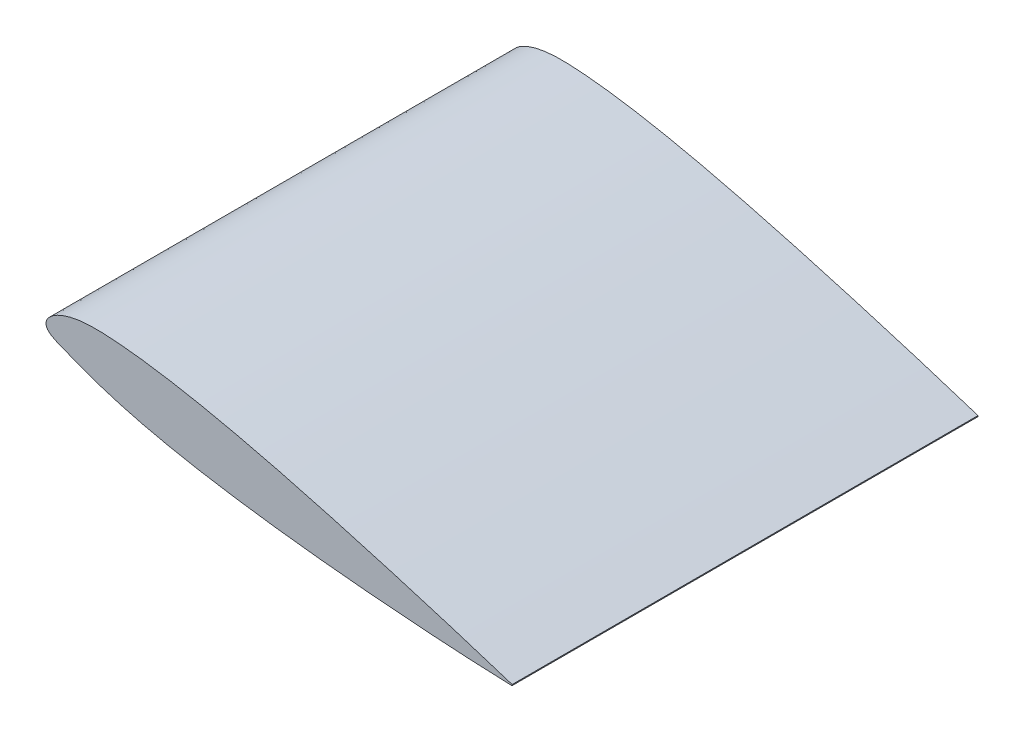
SolidWorks part; units mm, degrees
ref_plane "Płaszczyzna przednia"
ref_plane "Płaszczyzna górna" through (0, 0, 0) normal (0, 1, 0) x (1, 0, 0)
ref_plane "Płaszczyzna prawa" through (0, 0, 0) normal (1, 0, 0) x (0, 0, -1)
curve "Krzywa1"
  spline degree 3 poles (1, 0.0013, 0) (0.9998, 0.0013, 0) (0.9989, 0.0014, 0) (0.9968, 0.0017, 0) (0.9934, 0.0022, 0) (0.9886, 0.0029, 0) (0.9826, 0.0038, 0) (0.9751, 0.0049, 0) (0.9664, 0.0061, 0) (0.9564, 0.0076, 0) (0.9452, 0.0092, 0) (0.9327, 0.0109, 0) (0.9191, 0.0128, 0) (0.9043, 0.0148, 0) (0.8884, 0.017, 0) (0.8714, 0.0192, 0) (0.8535, 0.0216, 0) (0.8346, 0.0241, 0) (0.8147, 0.0266, 0) (0.794, 0.0292, 0) (0.7725, 0.0318, 0) (0.7503, 0.0345, 0) (0.7273, 0.0373, 0) (0.7038, 0.04, 0) (0.6797, 0.0427, 0) (0.6551, 0.0454, 0) (0.6301, 0.0481, 0) (0.6047, 0.0508, 0) (0.5791, 0.0533, 0) (0.5532, 0.0558, 0) (0.5272, 0.0582, 0) (0.5011, 0.0605, 0) (0.475, 0.0626, 0) (0.449, 0.0646, 0) (0.4231, 0.0664, 0) (0.3975, 0.068, 0) (0.3721, 0.0694, 0) (0.347, 0.0706, 0) (0.3224, 0.0715, 0) (0.2982, 0.0722, 0) (0.2746, 0.0726, 0) (0.2516, 0.0727, 0) (0.2293, 0.0725, 0) (0.2078, 0.072, 0) (0.187, 0.0713, 0) (0.1671, 0.0702, 0) (0.148, 0.0689, 0) (0.1298, 0.0672, 0) (0.1123, 0.0653, 0) (0.0953, 0.0628, 0) (0.0792, 0.0596, 0) (0.064, 0.0557, 0) (0.0502, 0.051, 0) (0.0378, 0.0457, 0) (0.027, 0.0399, 0) (0.018, 0.0338, 0) (0.0107, 0.0276, 0) (0.0052, 0.0214, 0) (0.0014, 0.0155, 0) (-0.0008, 0.0099, 0) (-0.0014, 0.0047, 0) (-0.0002, -0.0001, 0) (0.0023, -0.0042, 0) (0.0062, -0.0076, 0) (0.0111, -0.0104, 0) (0.017, -0.0128, 0) (0.0238, -0.0149, 0) (0.0314, -0.0168, 0) (0.0399, -0.0186, 0) (0.0492, -0.0205, 0) (0.0594, -0.0225, 0) (0.0706, -0.0247, 0) (0.0828, -0.027, 0) (0.0963, -0.0296, 0) (0.1112, -0.0323, 0) (0.1277, -0.035, 0) (0.1455, -0.0374, 0) (0.1644, -0.0397, 0) (0.1843, -0.0417, 0) (0.205, -0.0435, 0) (0.2265, -0.045, 0) (0.2488, -0.0462, 0) (0.2718, -0.0472, 0) (0.2954, -0.0479, 0) (0.3196, -0.0484, 0) (0.3443, -0.0486, 0) (0.3694, -0.0486, 0) (0.3948, -0.0484, 0) (0.4206, -0.0479, 0) (0.4466, -0.0473, 0) (0.4727, -0.0464, 0) (0.4989, -0.0454, 0) (0.5251, -0.0442, 0) (0.5512, -0.0429, 0) (0.5772, -0.0415, 0) (0.603, -0.0399, 0) (0.6285, -0.0382, 0) (0.6536, -0.0364, 0) (0.6784, -0.0346, 0) (0.7026, -0.0327, 0) (0.7262, -0.0307, 0) (0.7493, -0.0287, 0) (0.7716, -0.0267, 0) (0.7932, -0.0247, 0) (0.814, -0.0227, 0) (0.834, -0.0207, 0) (0.853, -0.0187, 0) (0.871, -0.0168, 0) (0.888, -0.0149, 0) (0.904, -0.0131, 0) (0.9188, -0.0114, 0) (0.9325, -0.0098, 0) (0.945, -0.0083, 0) (0.9563, -0.0069, 0) (0.9663, -0.0056, 0) (0.9751, -0.0045, 0) (0.9825, -0.0036, 0) (0.9886, -0.0028, 0) (0.9934, -0.0021, 0) (0.9968, -0.0017, 0) (0.9988, -0.0014, 0) (0.9998, -0.0013, 0) (1, -0.0013, 0) knots 0 0 0 0 0.000339 0.001354 0.003042 0.0054 0.008419 0.012092 0.016408 0.021354 0.026917 0.033081 0.039829 0.047141 0.054998 0.063377 0.072255 0.081607 0.091408 0.101629 0.112244 0.123222 0.134533 0.146147 0.15803 0.170151 0.182475 0.19497 0.2076 0.220332 0.233129 0.245957 0.258782 0.271567 0.284279 0.296882 0.309343 0.321628 0.333704 0.34554 0.357105 0.368367 0.379298 0.389869 0.400055 0.40983 0.419169 0.428054 0.436681 0.445097 0.45319 0.460863 0.468035 0.474639 0.480626 0.485963 0.490636 0.494656 0.49806 0.500929 0.503404 0.505691 0.507977 0.510416 0.513148 0.516239 0.519714 0.523574 0.527822 0.532466 0.537535 0.543075 0.549152 0.555845 0.563238 0.571416 0.580295 0.589636 0.599413 0.609602 0.620179 0.631116 0.642386 0.65396 0.665807 0.677897 0.690197 0.702675 0.715296 0.728027 0.740833 0.75368 0.766531 0.779352 0.792108 0.804762 0.817281 0.829629 0.841773 0.853679 0.865313 0.876645 0.887642 0.898273 0.908511 0.918326 0.92769 0.936579 0.944968 0.952833 0.960152 0.966905 0.973073 0.978639 0.983588 0.987905 0.991579 0.994599 0.996957 0.998646 0.999661 1 1 1 1
sketch "Szkic1" plane through (0, 0, 0) normal (0, 0, 1) x (1, 0, 0)
  line L0 (500.2365, -86.8225) -> (500.0145, -88.081)
  line L1 (500.1255, -87.4518) -> (0, 0) construction
  line L2 (6.055, 34.3399) -> (506.055, -53.8236) construction
  line L3 (6.055, 34.3399) -> (-4.5668, -25.8996) construction
  line L4 (-4.5668, -25.8996) -> (495.4332, -114.0631) construction
  line L5 (506.055, -53.8236) -> (495.4332, -114.0631) construction
  line L6 (0, 0) -> (-446.2529, 0) construction
  spline S1 degree 3 poles (500.2365, -86.8225) (476.503, -79.1176) (435.9073, -66.3525) (379.6351, -49.4321) (330.5145, -35.2103) (285.391, -22.7369) (243.0357, -11.7105) (204.9804, -2.4982) (171.8038, 4.7449) (143.8536, 10.1266) (121.2563, 13.9344) (103.2225, 16.4662) (89.5425, 18.0386) (79.9179, 18.9721) (70.6714, 19.6785) (61.7312, 20.1885) (53.0506, 20.387) (44.6983, 20.1711) (36.8008, 19.4846) (29.4786, 18.3169) (22.8393, 16.7003) (16.9702, 14.7008) (11.9337, 12.4062) (7.766, 9.9129) (4.4783, 7.3127) (2.0618, 4.6803) (0.4984, 2.0634) (-0.2126, -0.5168) (-0.0548, -2.9921) (0.8899, -5.2646) (2.5239, -7.2882) (4.7406, -9.1051) (7.4819, -10.7884) (10.7039, -12.4018) (14.3706, -14.003) (18.4574, -15.6451) (22.9574, -17.3754) (27.8856, -19.2351) (35.4451, -22.0705) (43.761, -25.1749) (52.968, -28.4954) (60.9562, -31.2334) (76.2265, -36.0534) (96.1258, -41.4724) (124.8888, -48.1756) (156.4178, -54.4498) (193.7907, -60.7106) (232.6126, -66.2455) (276.1309, -71.5852) (322.7828, -76.4383) (373.8186, -80.8845) (426.8549, -84.6598) (468.9302, -86.8921) (493.8831, -87.8637) (499.5472, -88.0646) (500.0145, -88.081) knots 0 0 0 0 0.072255 0.123222 0.170151 0.220332 0.258782 0.296882 0.333704 0.357105 0.379298 0.400055 0.40983 0.419169 0.428054 0.436681 0.445097 0.45319 0.460863 0.468035 0.474639 0.480626 0.485963 0.490636 0.494656 0.49806 0.500929 0.503404 0.505691 0.507977 0.510416 0.513148 0.516239 0.519714 0.523574 0.527822 0.532466 0.537535 0.543075 0.555845 0.563238 0.571416 0.580295 0.609602 0.631116 0.665807 0.702675 0.740833 0.779352 0.829629 0.876645 0.92769 0.983588 0.998646 1 1 1 1
  dimension "D1" = 90
  dimension "D2" = 90
  dimension "D3" = 90
  dimension "D4" = 500
  dimension "D5" = 80
extrude "Dodanie-wyciągnięcie1" add sketch "Szkic1" along normal blind 500
equation "\"kąt natarcia\"= 10"
equation "\"D5@Szkic1\"= 90 - \"kąt natarcia\""
